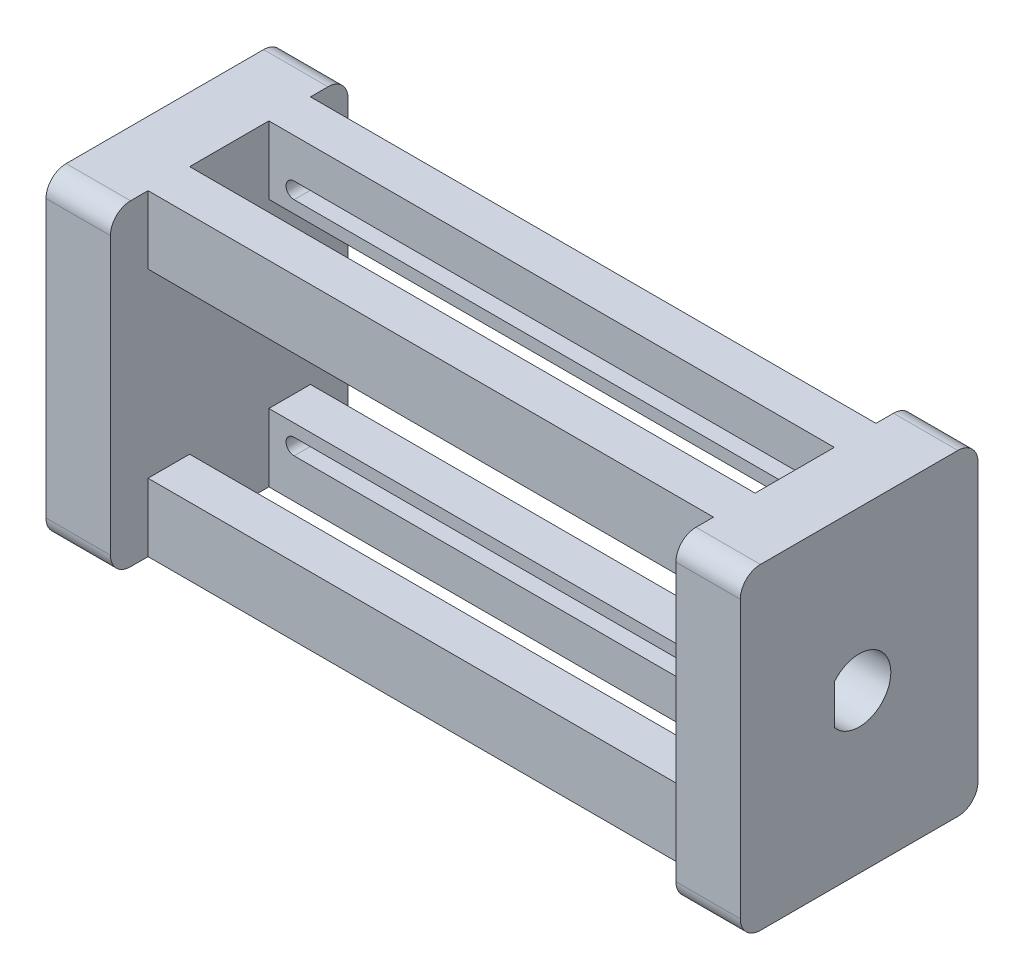
SolidWorks part; units mm, degrees
ref_plane "Front Plane" through (0, 0, 0) normal (0, 0, 1) x (1, 0, 0)
ref_plane "Top Plane" through (0, 0, 0) normal (0, 1, 0) x (1, 0, 0)
ref_plane "Right Plane" through (0, 0, 0) normal (1, 0, 0) x (0, 0, -1)
sketch "Sketch1" plane through (0, 0, 0) normal (0, 0, 1) x (1, 0, 0)
  line L1 (40, -20) -> (-40, -20)
  line L2 (40, -20) -> (40, 20)
  line L3 (40, 20) -> (-40, 20)
  line L4 (-40, -20) -> (-40, 20)
  line L5 (40, -20) -> (-40, 20) construction
  line L6 (40, 20) -> (-40, -20) construction
  point P0 (0, 0)
  dimension "D1" = 80
  dimension "D2" = 40
extrude "Boss-Extrude1" add sketch "Sketch1" along normal blind 20.5
sketch "Sketch2" plane through (0, 0, 20.5) normal (0, 0, 1) x (1, 0, 0)
  line L1 (33.3666, -11.427) -> (-33.3666, -11.427)
  line L2 (33.3666, -11.427) -> (33.3666, 11.427)
  line L3 (33.3666, 11.427) -> (-33.3666, 11.427)
  line L4 (-33.3666, -11.427) -> (-33.3666, 11.427)
  line L5 (33.3666, -11.427) -> (-33.3666, 11.427) construction
  line L6 (33.3666, 11.427) -> (-33.3666, -11.427) construction
  point P0 (0, 0)
  dimension "D1" = 66.7332
  dimension "D2" = 22.854
extrude "Cut-Extrude1" cut sketch "Sketch2" against normal through all
sketch "Sketch3" plane through (40, 0, 0) normal (1, 0, 0) x (0, 0, -1)
  line L4 (-20.5, 20) -> (0, 20) construction
  line L5 (-25.25, 20) -> (4.75, 20)
  line L6 (-25.25, 20) -> (-25.25, -20)
  line L7 (-25.25, -20) -> (4.75, -20)
  line L8 (4.75, 20) -> (4.75, -20)
  line L9 (-20.5, -20) -> (0, -20) construction
  point P8 (-10.25, 20)
  point P9 (-10.25, 20)
  dimension "D1" = 30
extrude "Boss-Extrude2" add sketch "Sketch3" along normal mid plane 7.62
mirror "Mirror1" about plane through (0, 0, 0) normal (1, 0, 0) of "Boss-Extrude2"
sketch "Sketch4" plane through (43.81, 0, 0) normal (1, 0, 0) x (0, 0, -1)
  line L1 (-25.25, 20) -> (-25.25, -20) construction
  line L3 (4.75, 20) -> (-25.25, 20) construction
  circle A0 centre (-10.25, 0) radius 4
  point P7 (-25.25, 0)
  point P9 (-10.25, 20)
  dimension "D1" = 8
extrude "Cut-Extrude2" cut sketch "Sketch4" against normal blind 5.8737
mirror "Mirror2" about plane through (0, 0, 0) normal (1, 0, 0) of "Cut-Extrude2"
sketch "Sketch6" plane through (0, -11.427, 0) normal (0, 1, 0) x (1, 0, 0)
  line L0 (-33.3666, 0) -> (-33.3666, -20.5) construction
  line L1 (33.3666, 0) -> (33.3666, -20.5) construction
  line L3 (-33.3666, -5.25) -> (-33.3666, -15.25)
  line L4 (33.3666, -5.25) -> (33.3666, -15.25)
  line L5 (33.3666, -15.25) -> (-33.3666, -15.25)
  line L6 (33.3666, -5.25) -> (-33.3666, -5.25)
  point P6 (33.3666, -10.25)
  point P7 (33.3666, -10.25)
  dimension "D1" = 10
extrude "Cut-Extrude4" cut sketch "Sketch6" against normal through all both and the other way through all
fillet "Fillet4" radius 2.54 8 edges at (-40, -20, 25.25) (-40, -20, -4.75) (-40, 20, 25.25) (-40, 20, -4.75) (40, -20, -4.75) (40, -20, 25.25) (40, 20, 25.25) (40, 20, -4.75)
sketch "Sketch7" plane through (0, 0, 0) normal (0, 0, -1) x (-1, 0, 0)
  line L0 (-32.5, 14) -> (32.5, 14) construction
  line L1 (-32.5, 15.016) -> (32.5, 15.016)
  line L2 (-32.5, 12.984) -> (32.5, 12.984)
  line L3 (-33.3666, 11.427) -> (33.3666, 11.427) construction
  arc A0 (-32.5, 15.016) -> (-32.5, 12.984) centre (-32.5, 14) ccw
  arc A1 (32.5, 12.984) -> (32.5, 15.016) centre (32.5, 14) ccw
  point P2 (0, 14)
  point P9 (0, 11.427)
  dimension "D2" = 1.016
  dimension "D1" = 2.573
  dimension "D3" = 65
extrude "Cut-Extrude5" cut sketch "Sketch7" against normal up to surface (5.25 mm away) up to face at (0, 15.7135, 5.25)
mirror "Mirror3" about plane through (0, 0, 0) normal (0, 1, 0) of "Cut-Extrude5"
sketch "Sketch8" plane through (43.81, 0, 0) normal (1, 0, 0) x (0, 0, -1)
  line L0 (-13.34, 2.54) -> (-13.34, -2.54)
  circle A0 centre (-10.25, 0) radius 4 construction
  circle A1 centre (-10.25, 0) radius 4 construction
  arc A2 (-13.34, 2.54) -> (-13.34, -2.54) centre (-10.25, 0) ccw
  dimension "D1" = 5.08
extrude "Boss-Extrude3" add sketch "Sketch8" against normal up to surface (5.8738 mm away) up to face at (37.9363, 0, 6.25)
sketch "Sketch9" plane through (-43.81, 0, 0) normal (-1, 0, 0) x (0, 0, 1)
  line L0 (13.34, 2.54) -> (13.34, -2.54)
  circle A0 centre (10.25, 0) radius 4 construction
  circle A1 centre (10.25, 0) radius 4 construction
  arc A2 (13.34, -2.54) -> (13.34, 2.54) centre (10.25, 0) ccw
  dimension "D1" = 5.08
extrude "Boss-Extrude4" add sketch "Sketch9" against normal up to surface (5.8738 mm away) up to face at (-37.9363, 0, 6.25)
sketch "Sketch10" plane through (33.3666, 0, 0) normal (-1, 0, 0) x (0, 0, 1)
  line L12 (20.5, 11.427) -> (15.25, 11.427)
  line L13 (15.25, 11.427) -> (15.25, 20)
  line L14 (15.25, 20) -> (5.25, 20)
  line L15 (5.25, 20) -> (5.25, 14.5304)
  line L16 (5.25, 11.427) -> (0, 11.427)
  line L17 (0, 11.427) -> (0, -11.427)
  line L18 (0, -11.427) -> (5.25, -11.427)
  line L19 (5.25, -11.427) -> (5.25, -13.4696)
  line L20 (5.25, -20) -> (15.25, -20)
  line L21 (15.25, -20) -> (15.25, -11.427)
  line L22 (15.25, -11.427) -> (20.5, -11.427)
  line L23 (20.5, -11.427) -> (20.5, 11.427)
  line L24 (20.5, 11.427) -> (15.25, 11.427)
  line L25 (15.25, 11.427) -> (15.25, 20)
  line L26 (15.25, 20) -> (5.25, 20)
  line L27 (5.25, 20) -> (5.25, 14.5304)
  line L28 (5.25, 11.427) -> (0, 11.427)
  line L29 (0, 11.427) -> (0, -11.427)
  line L30 (0, -11.427) -> (5.25, -11.427)
  line L31 (5.25, -11.427) -> (5.25, -13.4696)
  line L32 (5.25, -20) -> (15.25, -20)
  line L33 (15.25, -20) -> (15.25, -11.427)
  line L34 (15.25, -11.427) -> (20.5, -11.427)
  line L35 (20.5, -11.427) -> (20.5, 11.427)
  line L40 (5.25, 14.5304) -> (5.25, 13.4696)
  line L41 (5.25, 14.5304) -> (5.25, 13.4696)
  line L42 (5.25, 13.4696) -> (5.25, 11.427)
  line L43 (5.25, 13.4696) -> (5.25, 11.427)
  line L44 (5.25, -13.4696) -> (5.25, -14.5304)
  line L45 (5.25, -13.4696) -> (5.25, -14.5304)
  line L46 (5.25, -14.5304) -> (5.25, -20)
  line L47 (5.25, -14.5304) -> (5.25, -20)
  dimension "D1" = 0
extrude "Cut-Extrude6" cut sketch "Sketch10" against normal up to surface (2.8234 mm away) up to face at (36.19, 0, 22.9954)
sketch "Sketch11" plane through (-33.3666, 0, 0) normal (1, 0, 0) x (0, 0, -1)
  line L12 (-20.5, -11.427) -> (-15.25, -11.427)
  line L13 (-15.25, -11.427) -> (-15.25, -20)
  line L14 (-15.25, -20) -> (-5.25, -20)
  line L15 (-5.25, -20) -> (-5.25, -14.5304)
  line L16 (-5.25, -11.427) -> (0, -11.427)
  line L17 (0, -11.427) -> (0, 11.427)
  line L18 (0, 11.427) -> (-5.25, 11.427)
  line L19 (-5.25, 11.427) -> (-5.25, 13.4696)
  line L20 (-5.25, 20) -> (-15.25, 20)
  line L21 (-15.25, 20) -> (-15.25, 11.427)
  line L22 (-15.25, 11.427) -> (-20.5, 11.427)
  line L23 (-20.5, 11.427) -> (-20.5, -11.427)
  line L24 (-20.5, -11.427) -> (-15.25, -11.427)
  line L25 (-15.25, -11.427) -> (-15.25, -20)
  line L26 (-15.25, -20) -> (-5.25, -20)
  line L27 (-5.25, -20) -> (-5.25, -14.5304)
  line L28 (-5.25, -11.427) -> (0, -11.427)
  line L29 (0, -11.427) -> (0, 11.427)
  line L30 (0, 11.427) -> (-5.25, 11.427)
  line L31 (-5.25, 11.427) -> (-5.25, 13.4696)
  line L32 (-5.25, 20) -> (-15.25, 20)
  line L33 (-15.25, 20) -> (-15.25, 11.427)
  line L34 (-15.25, 11.427) -> (-20.5, 11.427)
  line L35 (-20.5, 11.427) -> (-20.5, -11.427)
  line L40 (-5.25, -14.5304) -> (-5.25, -13.4696)
  line L41 (-5.25, -14.5304) -> (-5.25, -13.4696)
  line L42 (-5.25, -13.4696) -> (-5.25, -11.427)
  line L43 (-5.25, -13.4696) -> (-5.25, -11.427)
  line L44 (-5.25, 13.4696) -> (-5.25, 14.5304)
  line L45 (-5.25, 13.4696) -> (-5.25, 14.5304)
  line L46 (-5.25, 14.5304) -> (-5.25, 20)
  line L47 (-5.25, 14.5304) -> (-5.25, 20)
  dimension "D1" = 0
extrude "Cut-Extrude7" cut sketch "Sketch11" against normal up to surface (2.8234 mm away) up to face at (-36.19, 0, -2.4954)
sketch "Sketch12" plane through (36.19, 0, 0) normal (-1, 0, 0) x (0, 0, 1)
  line L20 (-4.75, 17.46) -> (-4.75, -17.46)
  line L21 (-2.21, -20) -> (0, -20)
  line L22 (0, -20) -> (0, -11.427)
  line L23 (0, -11.427) -> (5.25, -11.427)
  line L24 (5.25, -11.427) -> (5.25, -20)
  line L25 (5.25, -20) -> (15.25, -20)
  line L26 (15.25, -20) -> (15.25, -11.427)
  line L27 (15.25, -11.427) -> (20.5, -11.427)
  line L28 (20.5, -11.427) -> (20.5, -20)
  line L29 (20.5, -20) -> (22.71, -20)
  line L30 (25.25, -17.46) -> (25.25, 17.46)
  line L31 (22.71, 20) -> (20.5, 20)
  line L32 (20.5, 20) -> (20.5, 11.427)
  line L33 (20.5, 11.427) -> (15.25, 11.427)
  line L34 (15.25, 11.427) -> (15.25, 20)
  line L35 (15.25, 20) -> (5.25, 20)
  line L36 (5.25, 20) -> (5.25, 11.427)
  line L37 (5.25, 11.427) -> (0, 11.427)
  line L38 (0, 11.427) -> (0, 20)
  line L39 (0, 20) -> (-2.21, 20)
  line L40 (-4.75, 17.46) -> (-4.75, -17.46)
  line L41 (-2.21, -20) -> (0, -20)
  line L42 (0, -20) -> (0, -11.427)
  line L43 (0, -11.427) -> (5.25, -11.427)
  line L44 (5.25, -11.427) -> (5.25, -20)
  line L45 (5.25, -20) -> (15.25, -20)
  line L46 (15.25, -20) -> (15.25, -11.427)
  line L47 (15.25, -11.427) -> (20.5, -11.427)
  line L48 (20.5, -11.427) -> (20.5, -20)
  line L49 (20.5, -20) -> (22.71, -20)
  line L50 (25.25, -17.46) -> (25.25, 17.46)
  line L51 (22.71, 20) -> (20.5, 20)
  line L52 (20.5, 20) -> (20.5, 11.427)
  line L53 (20.5, 11.427) -> (15.25, 11.427)
  line L54 (15.25, 11.427) -> (15.25, 20)
  line L55 (15.25, 20) -> (5.25, 20)
  line L56 (5.25, 20) -> (5.25, 11.427)
  line L57 (5.25, 11.427) -> (0, 11.427)
  line L58 (0, 11.427) -> (0, 20)
  line L59 (0, 20) -> (-2.21, 20)
  arc A4 (-4.75, -17.46) -> (-2.21, -20) centre (-2.21, -17.46) ccw
  arc A5 (22.71, -20) -> (25.25, -17.46) centre (22.71, -17.46) ccw
  arc A6 (25.25, 17.46) -> (22.71, 20) centre (22.71, 17.46) ccw
  arc A7 (-2.21, 20) -> (-4.75, 17.46) centre (-2.21, 17.46) ccw
  arc A8 (-4.75, -17.46) -> (-2.21, -20) centre (-2.21, -17.46) ccw
  arc A9 (22.71, -20) -> (25.25, -17.46) centre (22.71, -17.46) ccw
  arc A10 (25.25, 17.46) -> (22.71, 20) centre (22.71, 17.46) ccw
  arc A11 (-2.21, 20) -> (-4.75, 17.46) centre (-2.21, 17.46) ccw
  dimension "D1" = 0
extrude "Boss-Extrude5" add sketch "Sketch12" along normal blind 0.508
sketch "Sketch13" plane through (-36.19, 0, 0) normal (1, 0, 0) x (0, 0, -1)
  line L20 (0, -20) -> (2.21, -20)
  line L21 (4.75, -17.46) -> (4.75, 17.46)
  line L22 (2.21, 20) -> (0, 20)
  line L23 (0, 20) -> (0, 11.427)
  line L24 (0, 11.427) -> (-5.25, 11.427)
  line L25 (-5.25, 11.427) -> (-5.25, 20)
  line L26 (-5.25, 20) -> (-15.25, 20)
  line L27 (-15.25, 20) -> (-15.25, 11.427)
  line L28 (-15.25, 11.427) -> (-20.5, 11.427)
  line L29 (-20.5, 11.427) -> (-20.5, 20)
  line L30 (-20.5, 20) -> (-22.71, 20)
  line L31 (-25.25, 17.46) -> (-25.25, -17.46)
  line L32 (-22.71, -20) -> (-20.5, -20)
  line L33 (-20.5, -20) -> (-20.5, -11.427)
  line L34 (-20.5, -11.427) -> (-15.25, -11.427)
  line L35 (-15.25, -11.427) -> (-15.25, -20)
  line L36 (-15.25, -20) -> (-5.25, -20)
  line L37 (-5.25, -20) -> (-5.25, -11.427)
  line L38 (-5.25, -11.427) -> (0, -11.427)
  line L39 (0, -11.427) -> (0, -20)
  line L40 (0, -20) -> (2.21, -20)
  line L41 (4.75, -17.46) -> (4.75, 17.46)
  line L42 (2.21, 20) -> (0, 20)
  line L43 (0, 20) -> (0, 11.427)
  line L44 (0, 11.427) -> (-5.25, 11.427)
  line L45 (-5.25, 11.427) -> (-5.25, 20)
  line L46 (-5.25, 20) -> (-15.25, 20)
  line L47 (-15.25, 20) -> (-15.25, 11.427)
  line L48 (-15.25, 11.427) -> (-20.5, 11.427)
  line L49 (-20.5, 11.427) -> (-20.5, 20)
  line L50 (-20.5, 20) -> (-22.71, 20)
  line L51 (-25.25, 17.46) -> (-25.25, -17.46)
  line L52 (-22.71, -20) -> (-20.5, -20)
  line L53 (-20.5, -20) -> (-20.5, -11.427)
  line L54 (-20.5, -11.427) -> (-15.25, -11.427)
  line L55 (-15.25, -11.427) -> (-15.25, -20)
  line L56 (-15.25, -20) -> (-5.25, -20)
  line L57 (-5.25, -20) -> (-5.25, -11.427)
  line L58 (-5.25, -11.427) -> (0, -11.427)
  line L59 (0, -11.427) -> (0, -20)
  arc A4 (2.21, -20) -> (4.75, -17.46) centre (2.21, -17.46) ccw
  arc A5 (4.75, 17.46) -> (2.21, 20) centre (2.21, 17.46) ccw
  arc A6 (-22.71, 20) -> (-25.25, 17.46) centre (-22.71, 17.46) ccw
  arc A7 (-25.25, -17.46) -> (-22.71, -20) centre (-22.71, -17.46) ccw
  arc A8 (2.21, -20) -> (4.75, -17.46) centre (2.21, -17.46) ccw
  arc A9 (4.75, 17.46) -> (2.21, 20) centre (2.21, 17.46) ccw
  arc A10 (-22.71, 20) -> (-25.25, 17.46) centre (-22.71, 17.46) ccw
  arc A11 (-25.25, -17.46) -> (-22.71, -20) centre (-22.71, -17.46) ccw
  dimension "D1" = 0
extrude "Boss-Extrude6" add sketch "Sketch13" along normal blind 0.508
